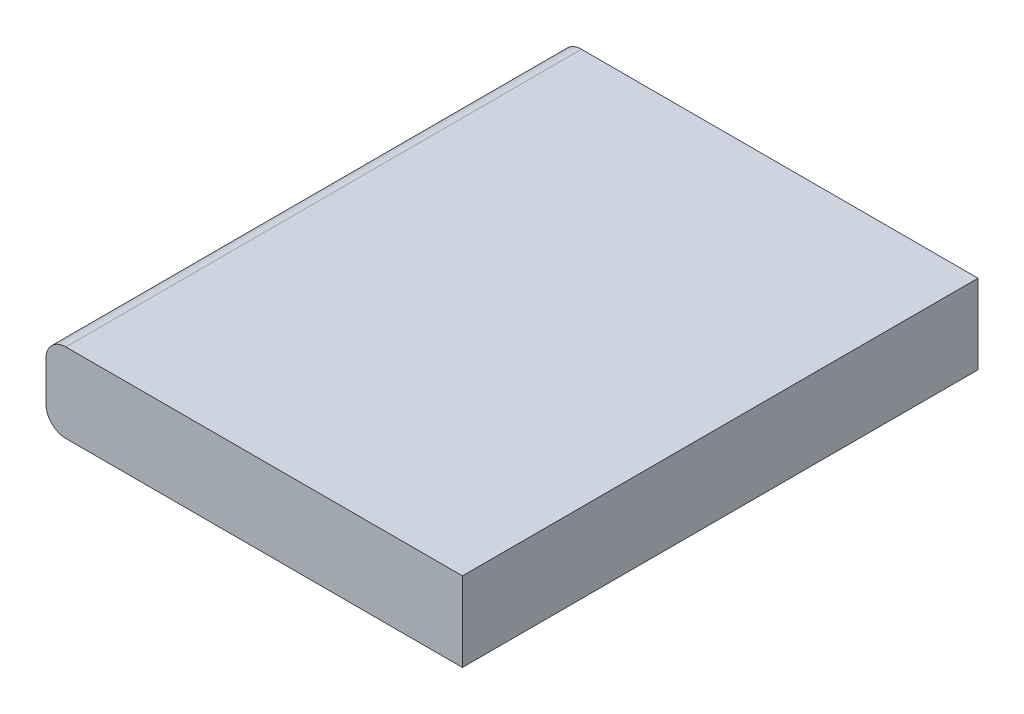
SolidWorks part; units mm, degrees
ref_plane "前视基准面" through (0, 0, 0) normal (0, 0, 1) x (1, 0, 0)
ref_plane "上视基准面" through (0, 0, 0) normal (0, 1, 0) x (1, 0, 0)
ref_plane "右视基准面" through (0, 0, 0) normal (1, 0, 0) x (0, 0, -1)
sketch "草图1" plane through (0, 0, 0) normal (0, 1, 0) x (1, 0, 0)
  line L0 (-1.1267, 0) -> (1.1267, 0) construction
  line L1 (0, 0.676) -> (0, -0.676) construction
  line L3 (-0.525, 0.65) -> (0.525, 0.65)
  line L4 (-0.525, 0.65) -> (-0.525, -0.65)
  line L5 (-0.525, -0.65) -> (0.525, -0.65)
  line L6 (0.525, 0.65) -> (0.525, -0.65)
  line L7 (-0.525, 0.65) -> (0.525, -0.65) construction
  line L8 (-0.525, -0.65) -> (0.525, 0.65) construction
  point P0 (0, 0)
  point P4 (0, 0)
  point P8 (0, 0)
  dimension "D1" = 1.05
  dimension "D2" = 1.3
extrude "凸台-拉伸1" add sketch "草图1" along normal blind 0.2
fillet "圆角5" radius 0.05 1 edges at (-0.525, 0.2, 0)
fillet "圆角6" radius 0.05 1 edges at (-0.525, 0, 0)
